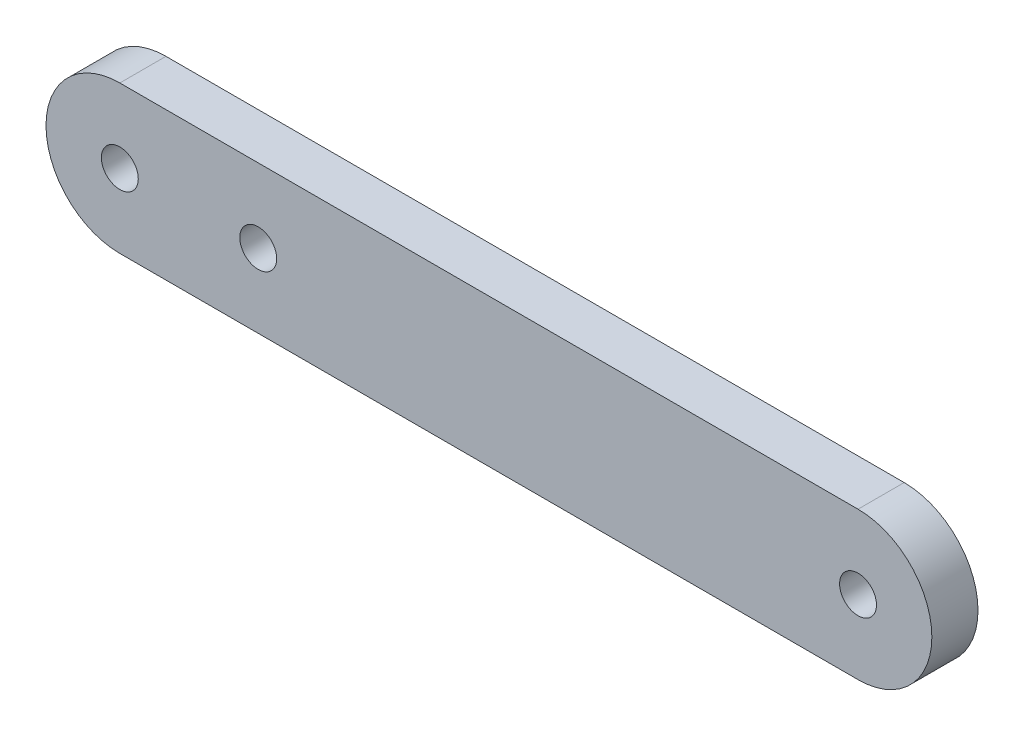
SolidWorks part; units mm, degrees
material "Thornel Mat VMA"
ref_plane "前视基准面" through (0, 0, 0) normal (0, 0, 1) x (1, 0, 0)
ref_plane "上视基准面" through (0, 0, 0) normal (0, 1, 0) x (1, 0, 0)
ref_plane "右视基准面" through (0, 0, 0) normal (1, 0, 0) x (0, 0, -1)
sketch "草图1" plane through (0, 0, 0) normal (0, 0, 1) x (1, 0, 0)
  line L0 (-40, 8) -> (40, 8)
  line L1 (-40, -8) -> (40, -8)
  line L2 (0, -55) -> (0, 55) construction
  arc A0 (-40, 8) -> (-40, -8) centre (-40, 0) ccw
  circle A1 centre (-40, 0) radius 2
  circle A2 centre (40, 0) radius 2
  arc A3 (40, 8) -> (40, -8) centre (40, 0) cw
  circle A7 centre (-25, 0) radius 2
  point P6 (0, 8)
  point P12 (0, -8)
  dimension "D1" = 40
  dimension "D2" = 4
  dimension "D3" = 8
  dimension "D6" = 4
  dimension "D7" = 15
extrude "凸台-拉伸1" add sketch "草图1" along normal blind 5
